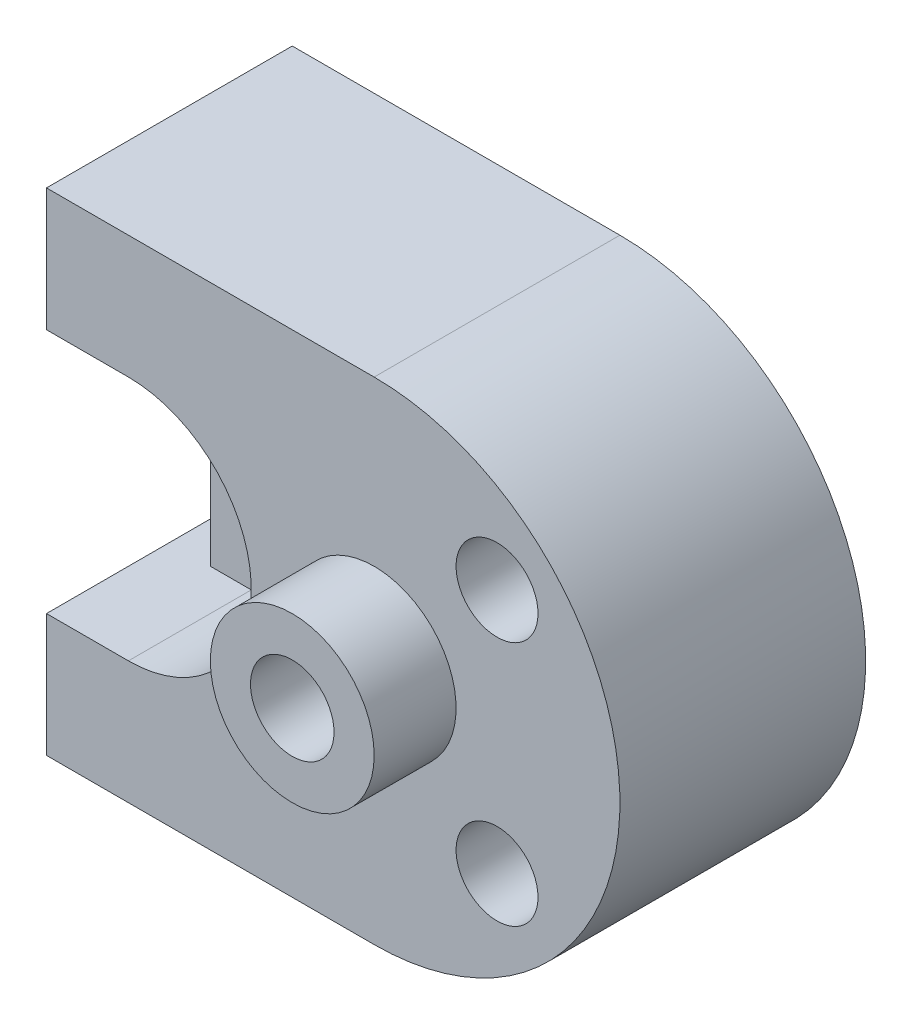
SolidWorks part; units mm, degrees
ref_plane "Front Plane" through (0, 0, 0) normal (0, 0, 1) x (1, 0, 0)
ref_plane "Top Plane" through (0, 0, 0) normal (0, 1, 0) x (1, 0, 0)
ref_plane "Right Plane" through (0, 0, 0) normal (1, 0, 0) x (0, 0, -1)
sketch "Sketch1" plane through (0, 0, 0) normal (0, 0, 1) x (1, 0, 0)
  line L0 (-40, 30) -> (-40, 15)
  line L1 (-40, 15) -> (-30, 15)
  line L2 (-30, -15) -> (-40, -15)
  line L3 (-40, -15) -> (-40, -30)
  line L4 (-40, -30) -> (0, -30)
  line L5 (-40, 30) -> (0, 30)
  arc A0 (-30, 15) -> (-30, -15) centre (-30, 0) cw
  arc A1 (0, 30) -> (0, -30) centre (0, 0) cw
  dimension "D6" = 15
  dimension "D1" = 40
  dimension "D2" = 40
  dimension "D3" = 15
  dimension "D4" = 15
  dimension "D5" = 10
extrude "Boss-Extrude1" add sketch "Sketch1" along normal blind 30
sketch "Sketch5" plane through (0, 0, 30) normal (0, 0, 1) x (1, 0, 0)
  line L0 (-30, 15) -> (-35, 15)
  line L1 (-30, -15) -> (-35, -15)
  line L2 (-35, -15) -> (-35, 15)
  arc A0 (-30, 15) -> (-30, -15) centre (-30, 0) cw
  arc A1 (-30, -15) -> (-30, 15) centre (-30, 0) ccw construction
  dimension "D1" = 5
  dimension "D2" = 5
extrude "Boss-Extrude3" add sketch "Sketch5" against normal blind 30
sketch "Sketch6" plane through (0, 0, 30) normal (0, 0, 1) x (1, 0, 0)
  line L0 (-35, 15) -> (-30, 15)
  line L1 (-35, -15) -> (-29.999, -15)
  line L2 (-35, -15) -> (-35, 15)
  arc A0 (-30, 15) -> (-29.999, -15) centre (-30, 0) cw
  dimension "D1" = 5
  dimension "D2" = 5.001
extrude "Cut-Extrude1" cut sketch "Sketch6" against normal blind 15
sketch "Sketch7" plane through (0, 0, 15) normal (0, 0, 1) x (1, 0, 0)
  line L0 (-35, 15) -> (-35, -15) construction
  line L1 (-40, 15) -> (-30, 15) construction
  circle A0 centre (-25, 0) radius 5
  dimension "D1" = 10
  dimension "D2" = 10
  dimension "D3" = 15
extrude "Cut-Extrude2" cut sketch "Sketch7" against normal blind 35
sketch "Sketch8" plane through (0, 0, 30) normal (0, 0, 1) x (1, 0, 0)
  circle A0 centre (0, 0) radius 10
  dimension "D1" = 20
extrude "Boss-Extrude4" add sketch "Sketch8" along normal blind 10
sketch "Sketch10" plane through (0, 0, 30) normal (0, 0, 1) x (1, 0, 0)
  circle A0 centre (15, 15) radius 5
  circle A1 centre (15, -15) radius 5
  dimension "D1" = 10
  dimension "D2" = 10
  dimension "D3" = 15
  dimension "D4" = 15
  dimension "D5" = 15
  dimension "D6" = 15
extrude "Cut-Extrude6" cut sketch "Sketch10" against normal blind 10
sketch "Sketch12" plane through (0, 0, 20) normal (0, 0, 1) x (1, 0, 0)
  circle A0 centre (15, 15) radius 2.5
  circle A1 centre (15, -15) radius 2.5
  dimension "D1" = 5
  dimension "D2" = 5
extrude "Cut-Extrude7" cut sketch "Sketch12" against normal blind 10
sketch "Sketch13" plane through (0, 0, 0) normal (0, 0, -1) x (-1, 0, 0)
  circle A0 centre (-15, 15) radius 5
  circle A1 centre (-15, -15) radius 5
extrude "Cut-Extrude8" cut sketch "Sketch13" against normal blind 10
hole_wizard "M12 Tapped Hole1" positions "3DSketch1" profile "Sketch14" tap size "M12" standard "ISO"
sketch3d "3DSketch1"
  line L0 (0, 0, 40) -> (0, 0, 30) construction
  point P0 (0, 0, 40)
sketch "Sketch14" plane through (0, 0, 40) normal (1, 0, 0) x (0, -1, 0)
  line L0 (0, 0) -> (0, 18.0644)
  line L1 (0, 18.0644) -> (5.1, 15)
  line L2 (5.1, 15) -> (5.1, 0)
  line L5 (5.1, 0) -> (0, 0)
  line L10 (0, 18.0644) -> (-5.1, 15) construction
  line L11 (0, -6.35) -> (0, 107.95) construction
  dimension "Tap Drill Dia." = 10.2
  dimension "Tap Drill Depth" = 15
  dimension "Drill Angle" = 118
cosmetic thread "Hole Thread1" parameters "D1"=15, "D2"=12
